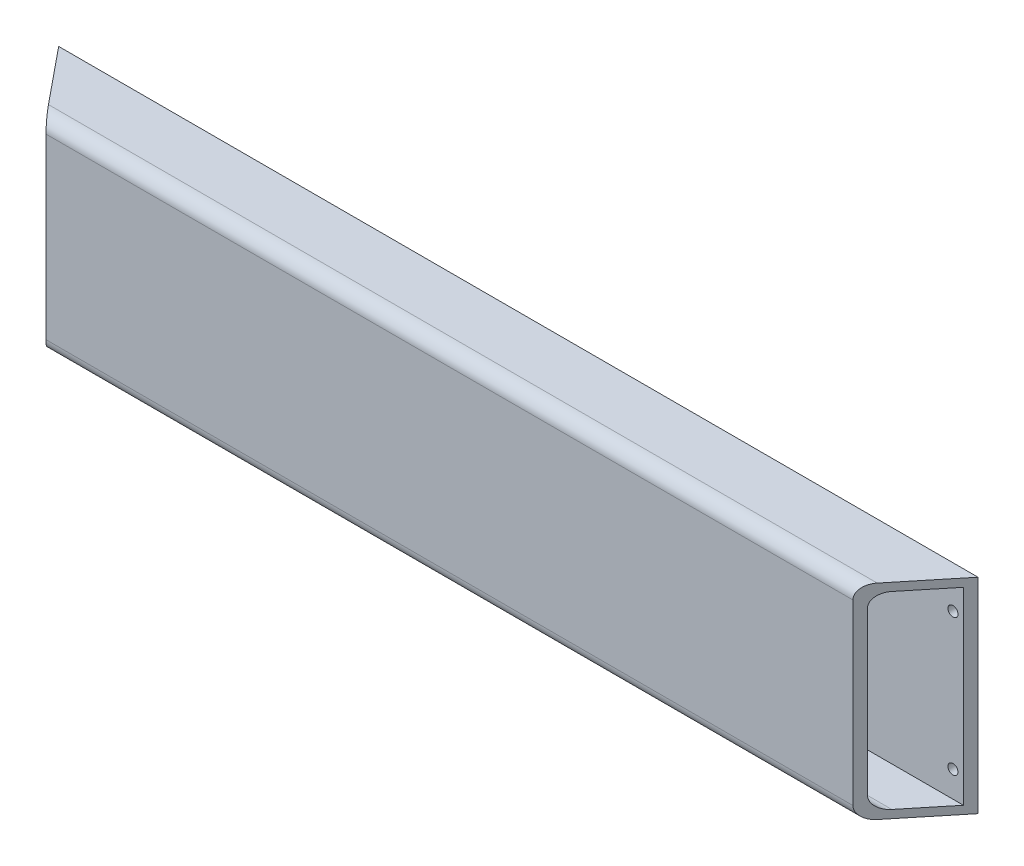
SolidWorks part; units mm, degrees
material "Cast Alloy Steel"
ref_plane "Front Plane" through (0, 0, 0) normal (0, 0, 1) x (1, 0, 0)
ref_plane "Top Plane" through (0, 0, 0) normal (0, 1, 0) x (1, 0, 0)
ref_plane "Right Plane" through (0, 0, 0) normal (1, 0, 0) x (0, 0, -1)
sketch "Sketch1" plane through (0, 0, 0) normal (0, 0, 1) x (1, 0, 0)
  line L1 (0, 0) -> (686.81, 0)
  line L2 (0, 0) -> (0, 153)
  line L3 (0, 153) -> (686.81, 153)
  line L4 (686.81, 0) -> (686.81, 153)
  dimension "D1" = 153
  dimension "D2" = 686.81
extrude "Boss-Extrude1" add sketch "Sketch1" along normal blind 51.46
ref_plane "Plane1" through (343.405, 0, 0) normal (-1, 0, 0) x (0, 0, 1)
sketch "Sketch2" plane through (0, 0, 0) normal (0, -1, 0) x (1, 0, 0)
  line L0 (0, 0) -> (42, 51.46)
  line L1 (0, 51.46) -> (686.81, 51.46) construction
  line L2 (42, 51.46) -> (-52.5787, 191.3517)
  line L3 (-52.5787, 191.3517) -> (-175.691, 25.73)
  line L4 (-175.691, 25.73) -> (0, 0)
  line L5 (686.81, 0) -> (644.81, 51.46)
  line L6 (644.81, 51.46) -> (843.6195, 127.9829)
  line L7 (843.6195, 127.9829) -> (686.81, 0)
  dimension "D1" = 42
  dimension "D2" = 42
extrude "Cut-Extrude1" cut sketch "Sketch2" against normal up to surface (153 mm away) up to face at (343.405, 153, 25.73)
shell "Shell1" thickness 6
sketch "Sketch3" plane through (0, 0, 6) normal (0, 0, 1) x (1, 0, 0)
  line L0 (686.81, 153) -> (0, 153) construction
  line L1 (0, 0) -> (686.81, 0) construction
  line L2 (686.81, 0) -> (686.81, 153) construction
  line L3 (0, 153) -> (0, 0) construction
  circle A0 centre (12.7, 25.4) radius 3.75
  circle A1 centre (12.7, 127.6) radius 3.75
  circle A2 centre (674.11, 25.4) radius 3.75
  circle A3 centre (674.11, 127.6) radius 3.75
  dimension "D5" = 7.5
  dimension "D1" = 25.4
  dimension "D2" = 25.4
  dimension "D3" = 12.7
  dimension "D4" = 12.7
extrude "Cut-Extrude2" cut sketch "Sketch3" against normal up to surface (6 mm away) up to face at (343.405, 76.5, 0)
fillet "Fillet1" radius 10 4 edges at (343.405, 0, 51.46) (343.405, 153, 51.46) (343.405, 6, 45.46) (343.405, 147, 45.46)
ref_plane "Plane2" through (0, 76.5, 0) normal (0, 1, 0) x (1, 0, 0)
